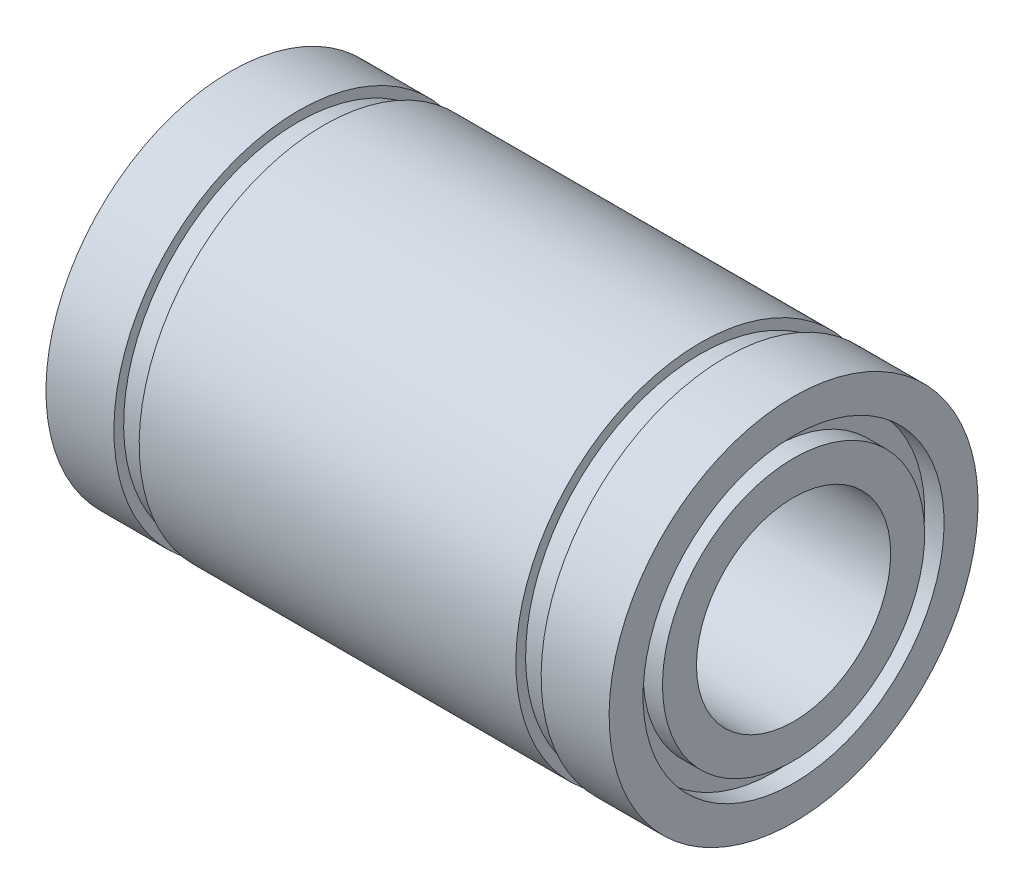
SolidWorks part; units mm, degrees
material "Ст3сп ГОСТ 535-2005"
ref_plane "Plano frontal" through (0, 0, 0) normal (0, 0, 1) x (1, 0, 0)
ref_plane "Plano superior" through (0, 0, 0) normal (0, 1, 0) x (1, 0, 0)
ref_plane "Plano direito" through (0, 0, 0) normal (1, 0, 0) x (0, 0, -1)
sketch "Esboço1" plane through (0, 0, 0) normal (0, 0, 1) x (1, 0, 0)
  line L0 (-14.5, 9.5) -> (-11, 9.5)
  line L1 (-11, 9.5) -> (-11, 9)
  line L2 (-11, 9) -> (-9.7, 9)
  line L3 (-9.7, 9) -> (-9.7, 9.5)
  line L4 (-9.7, 9.5) -> (9.7, 9.5)
  line L5 (9.7, 9.5) -> (9.7, 9)
  line L6 (9.7, 9) -> (11, 9)
  line L7 (11, 9) -> (11, 9.5)
  line L8 (11, 9.5) -> (14.5, 9.5)
  line L9 (14.5, 9.5) -> (14.5, 7.75)
  line L10 (14.5, 5) -> (-14.5, 5)
  line L11 (-14.5, 5) -> (-14.5, 6.75)
  line L12 (0, 5) -> (0, 0) construction
  line L13 (0, 0) -> (-86.5, 0) construction
  line L14 (-14.5, 7.75) -> (-14.5, 9.5)
  line L15 (-14.5, 7.75) -> (-13.5, 7.75)
  line L16 (14.5, 6.75) -> (14.5, 5)
  line L17 (-13.5, 7.75) -> (-13.5, 6.75)
  line L18 (-13.5, 6.75) -> (-14.5, 6.75)
  line L19 (14.5, 7.75) -> (13.5, 7.75)
  line L21 (14.5, 6.75) -> (13.5, 6.75)
  line L22 (13.5, 7.75) -> (13.5, 6.75)
  dimension "D1" = 29
  dimension "D2" = 22
  dimension "D3" = 1.3
  dimension "D4" = 10
  dimension "D5" = 19
  dimension "D6" = 18
  dimension "D7" = 1
  dimension "D8" = 1
  dimension "D9" = 1
  dimension "D10" = 1
revolve "Revolução1" add sketch "Esboço1" angle 360 about L13
